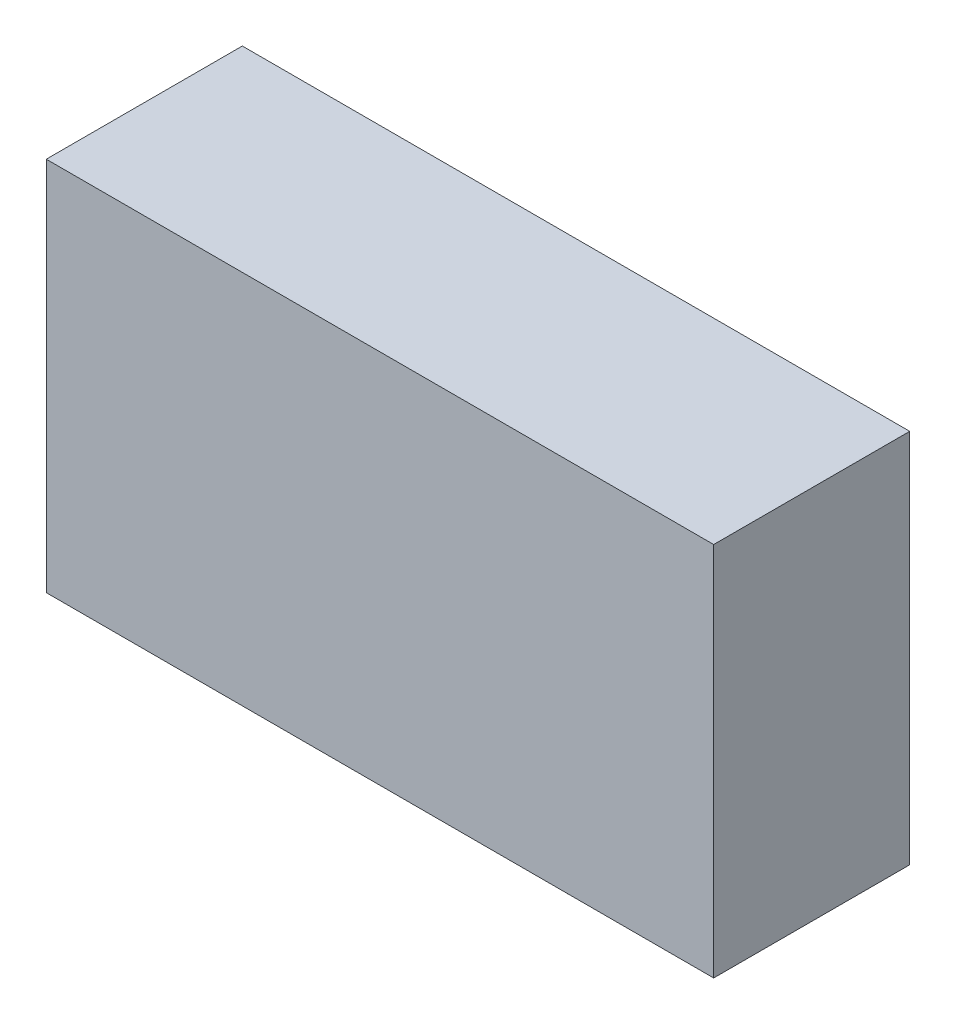
SolidWorks part; units mm, degrees
ref_plane "前视基准面" through (0, 0, 0) normal (0, 0, 1) x (1, 0, 0)
ref_plane "上视基准面" through (0, 0, 0) normal (0, 1, 0) x (1, 0, 0)
ref_plane "右视基准面" through (0, 0, 0) normal (1, 0, 0) x (0, 0, -1)
other "Configuration Table"
sketch "草图1" plane through (0, 0, 0) normal (0, 0, 1) x (1, 0, 0)
  line L1 (0, 0) -> (8, 0)
  line L2 (0, 0) -> (0, 4.5)
  line L3 (0, 4.5) -> (8, 4.5)
  line L4 (8, 0) -> (8, 4.5)
  dimension "D1" = 4.5
  dimension "D2" = 8
extrude "凸台-拉伸1" add sketch "草图1" along normal blind 2.35
